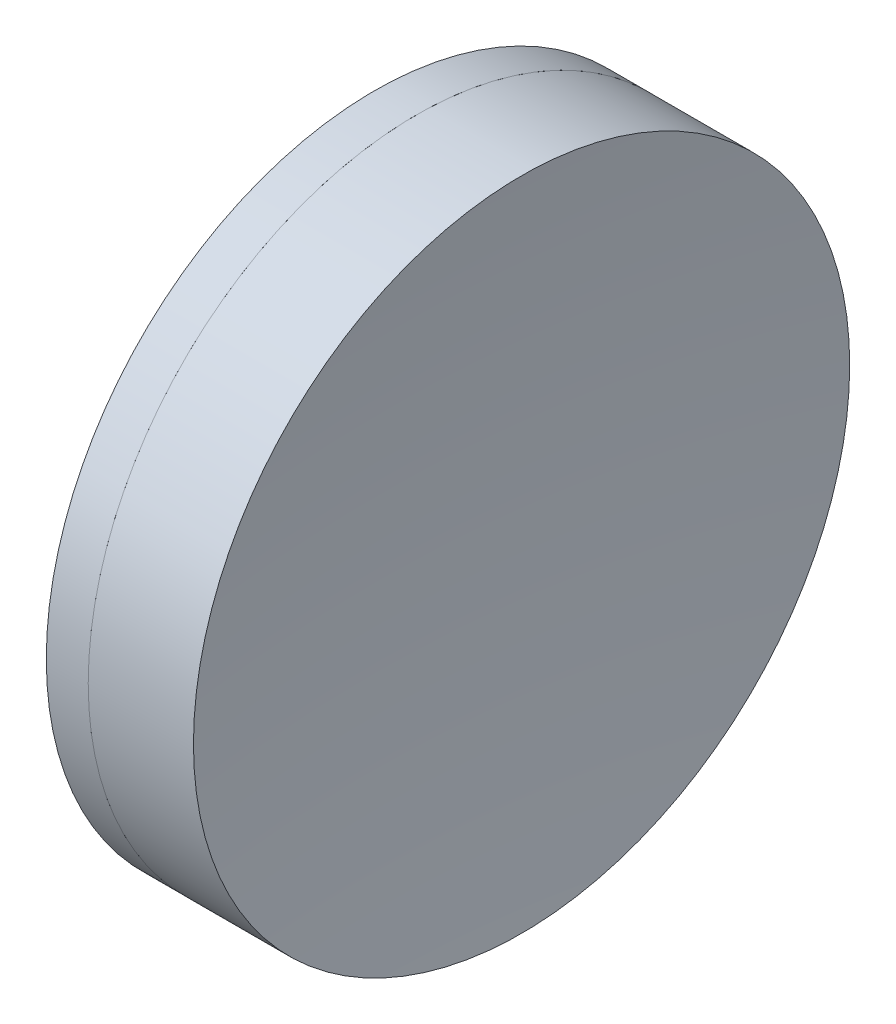
SolidWorks part; units mm, degrees
ref_plane "前视基准面" through (0, 0, 0) normal (0, 0, 1) x (1, 0, 0)
ref_plane "上视基准面" through (0, 0, 0) normal (0, 1, 0) x (1, 0, 0)
ref_plane "右视基准面" through (0, 0, 0) normal (1, 0, 0) x (0, 0, -1)
sketch "草图1" plane through (0, 0, 0) normal (0, 1, 0) x (1, 0, 0)
  line L0 (-0.8161, 0) -> (153.1215, 0) construction
  line L1 (141.9195, -25.4) -> (145.1648, -25.4)
  line L2 (141.9195, 25.4) -> (145.1648, 25.4)
  arc A0 (145.1648, -25.4) -> (145.1648, 25.4) centre (61.3594, 0) ccw
  arc A1 (141.9195, 25.4) -> (141.9195, -25.4) centre (204.0694, 0) ccw
  point P4 (153.1215, 0)
  point P10 (136.9294, 0)
  point P11 (148.9294, 0)
  dimension "D3" = 67.14
  dimension "D4" = 87.57
  dimension "D1" = 25.4
  dimension "D2" = 25.4
  dimension "D5" = 12
revolve "旋转1" add sketch "草图1" angle 360 about L0
sketch "草图2" plane through (0, 0, 0) normal (0, 1, 0) x (1, 0, 0)
  line L0 (-0.5519, 0) -> (162.8134, 0) construction
  line L2 (145.1648, 25.4) -> (153.3105, 25.4)
  line L3 (145.1648, -25.4) -> (153.3105, -25.4)
  arc A0 (153.3105, 25.4) -> (153.3105, -25.4) centre (386.1994, 0) ccw
  arc A1 (145.1648, -25.4) -> (145.1648, 25.4) centre (61.3594, 0) ccw construction
  arc A2 (145.1648, -25.4) -> (145.1648, 25.4) centre (61.3594, 0) ccw
  point P4 (148.9294, 0)
  point P8 (151.9294, 0)
  dimension "D1" = 234.27
  dimension "D2" = 3
revolve "旋转2" add sketch "草图2" angle 360 about L0
